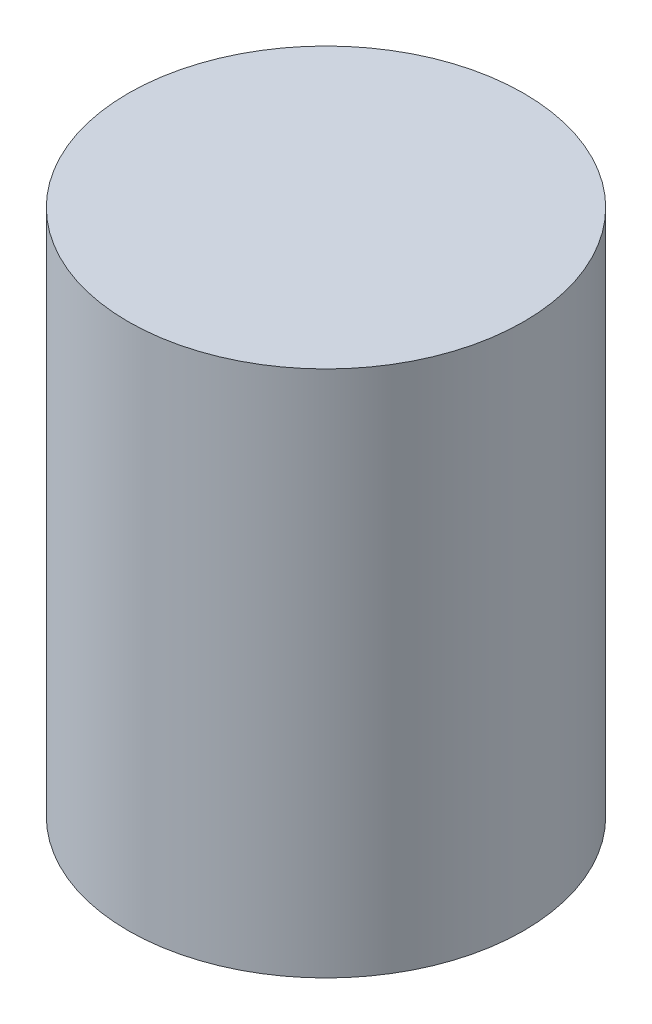
SolidWorks part; units mm, degrees
ref_plane "Front" through (0, 0, 0) normal (0, 0, 1) x (1, 0, 0)
ref_plane "Top" through (0, 0, 0) normal (0, 1, 0) x (1, 0, 0)
ref_plane "Right" through (0, 0, 0) normal (1, 0, 0) x (0, 0, -1)
sketch "草图1" plane through (0, 0, 0) normal (0, 1, 0) x (1, 0, 0)
  circle A0 centre (0, 0) radius 30
  dimension "D1" = 60
extrude "凸台-拉伸1" add sketch "草图1" along normal blind 80
